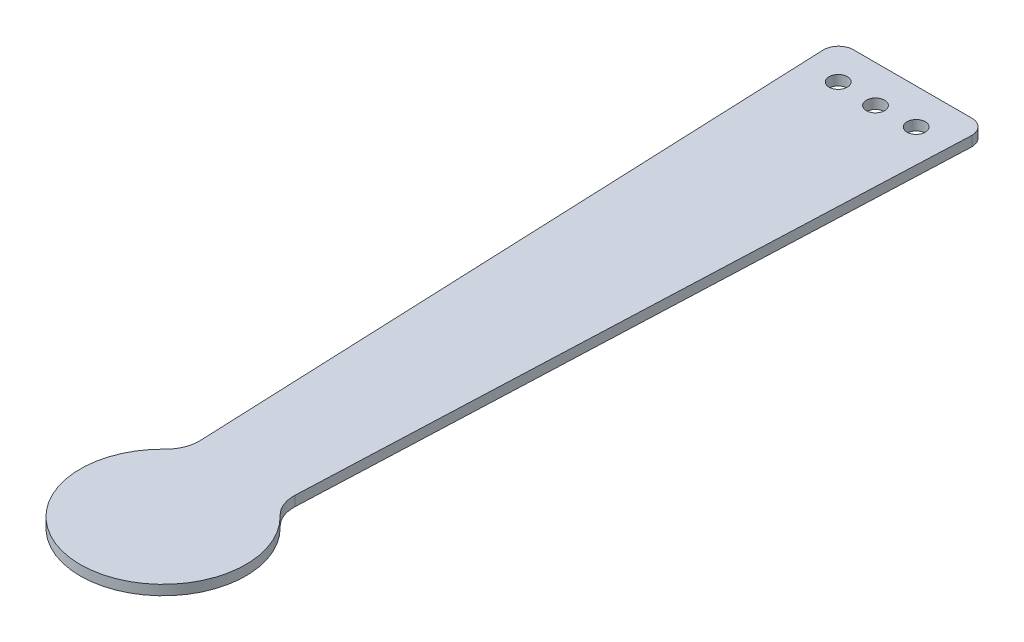
SolidWorks part; units mm, degrees
ref_plane "Front Plane" through (0, 0, 0) normal (0, 0, 1) x (1, 0, 0)
ref_plane "Top Plane" through (0, 0, 0) normal (0, 1, 0) x (1, 0, 0)
ref_plane "Right Plane" through (0, 0, 0) normal (1, 0, 0) x (0, 0, -1)
sketch "Sketch1" plane through (0, 0, 0) normal (0, 1, 0) x (1, 0, 0)
  line L5 (0, 0) -> (0, -251.2187) construction
  line L6 (-24.9919, -226.2187) -> (24.9919, -226.2187) construction
  line L7 (-18.1652, 0) -> (18.1652, 0)
  line L8 (22.3762, -4.4951) -> (14.2953, -200.741)
  line L9 (-22.3762, -4.4951) -> (-14.2953, -200.741)
  circle A41 centre (0, -226.2187) radius 5
  circle A42 centre (0, -226.2187) radius 15
  circle A43 centre (0, -226.2187) radius 24.9919
  arc A44 (17.5067, 0) -> (22.3762, -4.4951) centre (17.8359, -4.5284) cw
  arc A45 (14.2953, -200.741) -> (17.4001, -208.2791) centre (24.2911, -201.0324) ccw
  arc A46 (-14.2953, -200.741) -> (-17.4001, -208.2791) centre (-24.2911, -201.0324) cw
  arc A47 (-17.5067, 0) -> (-22.3762, -4.4951) centre (-17.8359, -4.5284) ccw
  circle A65 centre (11.7742, -10.705) radius 2.75
  circle A66 centre (0.0081, -11.2187) radius 2.75
  circle A67 centre (-11.7579, -10.705) radius 2.75
  point P0 (0, 0)
  point P104 (0, 0)
  dimension "D1" = 215
extrude "Boss-Extrude3" add sketch "Sketch1" along normal blind 3 contours L7 A47 L9 A46 A43 A45 L8 A44 A67 A66 A65 | A43 A46 A45 A42 | A42 A41 | A41
sketch "Sketch3" plane through (0, 3, 0) normal (0, 1, 0) x (1, 0, 0)
  line L0 (-25, -226.2187) -> (25, -226.2187)
  line L1 (0, -201.2187) -> (0, -251.2187)
  circle A0 centre (0, -226.2187) radius 15
  circle A1 centre (0, -226.2187) radius 5
  circle A2 centre (0, -226.2187) radius 25
  arc A3 (-11.7579, -10.705) -> (11.7742, -10.705) centre (0.0081, 123.7813) ccw
